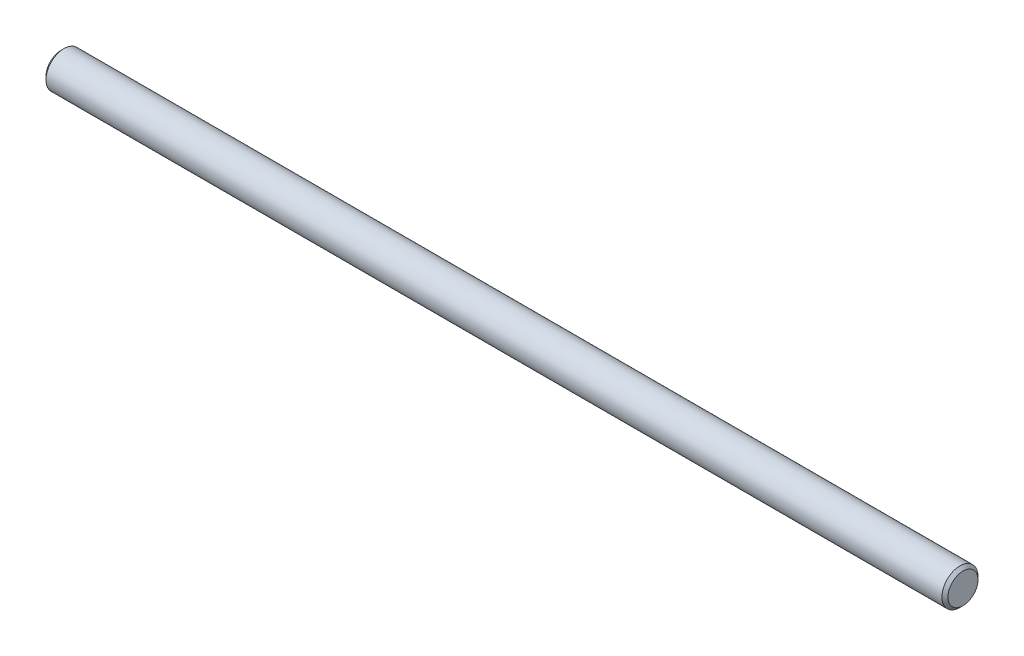
SolidWorks part; units mm, degrees
ref_plane "Front Plane" through (0, 0, 0) normal (0, 0, 1) x (1, 0, 0)
ref_plane "Top Plane" through (0, 0, 0) normal (0, 1, 0) x (1, 0, 0)
ref_plane "Right Plane" through (0, 0, 0) normal (1, 0, 0) x (0, 0, -1)
sketch "Sketch1" plane through (0, 0, 0) normal (1, 0, 0) x (0, 0, -1)
  circle A0 centre (0, 0) radius 6
  dimension "D1" = 12
extrude "Boss-Extrude1" add sketch "Sketch1" along normal blind 300
chamfer "Chamfer1" distance 1 angle 45 2 edges at (300, 0, -6) (0, 0, -6)
